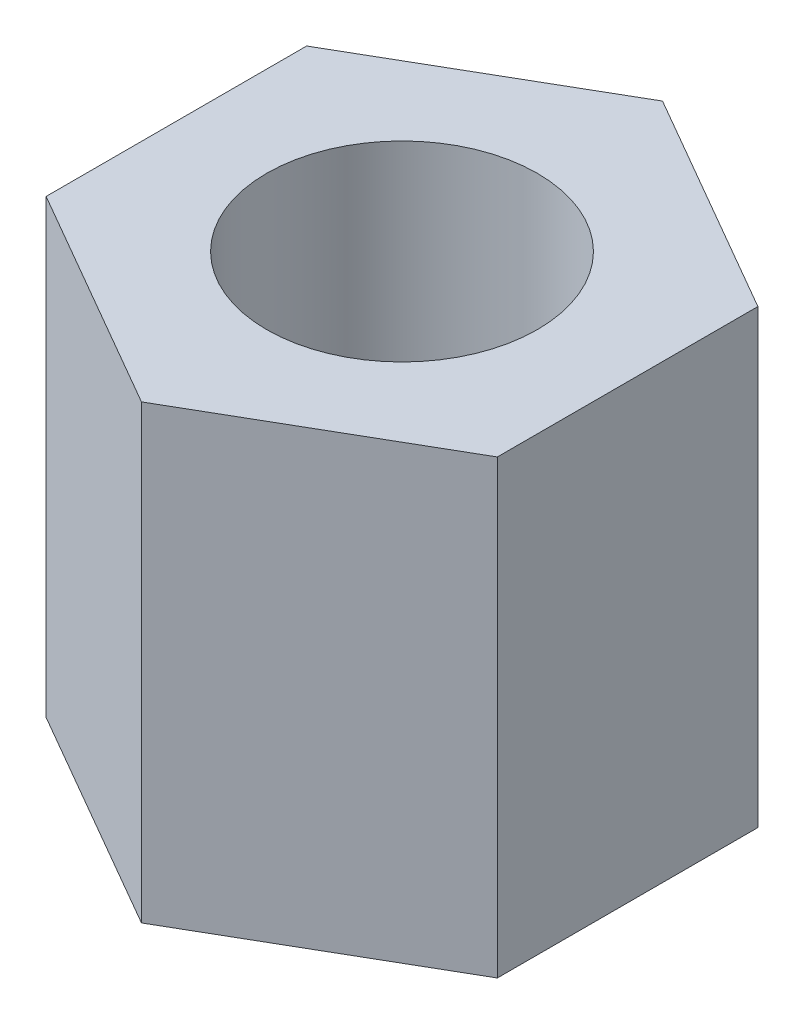
SolidWorks part; units mm, degrees
ref_plane "Front Plane" through (0, 0, 0) normal (0, 0, 1) x (1, 0, 0)
ref_plane "Top Plane" through (0, 0, 0) normal (0, 1, 0) x (1, 0, 0)
ref_plane "Right Plane" through (0, 0, 0) normal (1, 0, 0) x (0, 0, -1)
sketch "Sketch1" plane through (0, 0, 0) normal (0, 1, 0) x (1, 0, 0)
  line L1 (0, -3.6662) -> (3.175, -1.8331)
  line L2 (3.175, -1.8331) -> (3.175, 1.8331)
  line L3 (3.175, 1.8331) -> (0, 3.6662)
  line L4 (0, 3.6662) -> (-3.175, 1.8331)
  line L5 (-3.175, 1.8331) -> (-3.175, -1.8331)
  line L6 (-3.175, -1.8331) -> (0, -3.6662)
  circle A0 centre (0, 0) radius 3.175 construction
  circle A1 centre (0, 0) radius 1.905
  dimension "D2" = 3.81
  dimension "D1" = 6.35
extrude "Boss-Extrude1" add sketch "Sketch1" along normal blind 6.35
